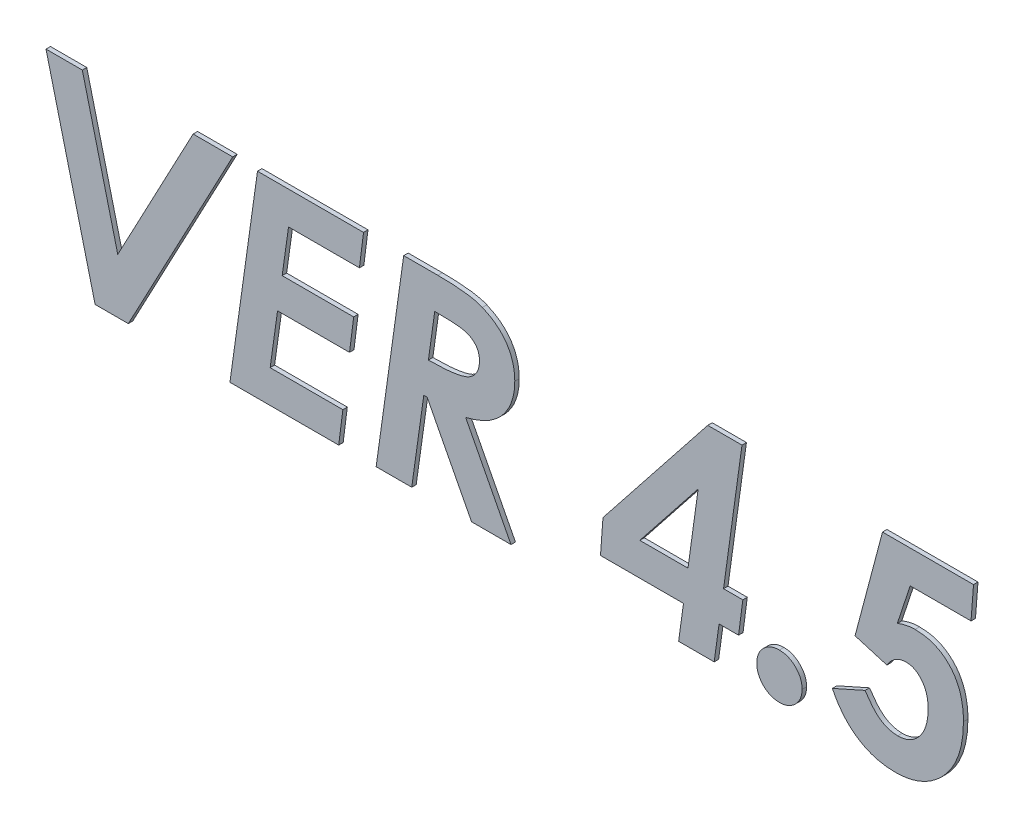
SolidWorks part; units mm, degrees
ref_plane "Front Plane" through (0, 0, 0) normal (0, 0, 1) x (1, 0, 0)
ref_plane "Top Plane" through (0, 0, 0) normal (0, 1, 0) x (1, 0, 0)
ref_plane "Right Plane" through (0, 0, 0) normal (1, 0, 0) x (0, 0, -1)
sketch "Sketch1" plane through (0, 0, 0) normal (0, 0, 1) x (1, 0, 0)
  text T0 "VER 4.5" font "Century Gothic" height 22
extrude "Boss-Extrude1" add sketch "Sketch1" along normal blind 0.5
